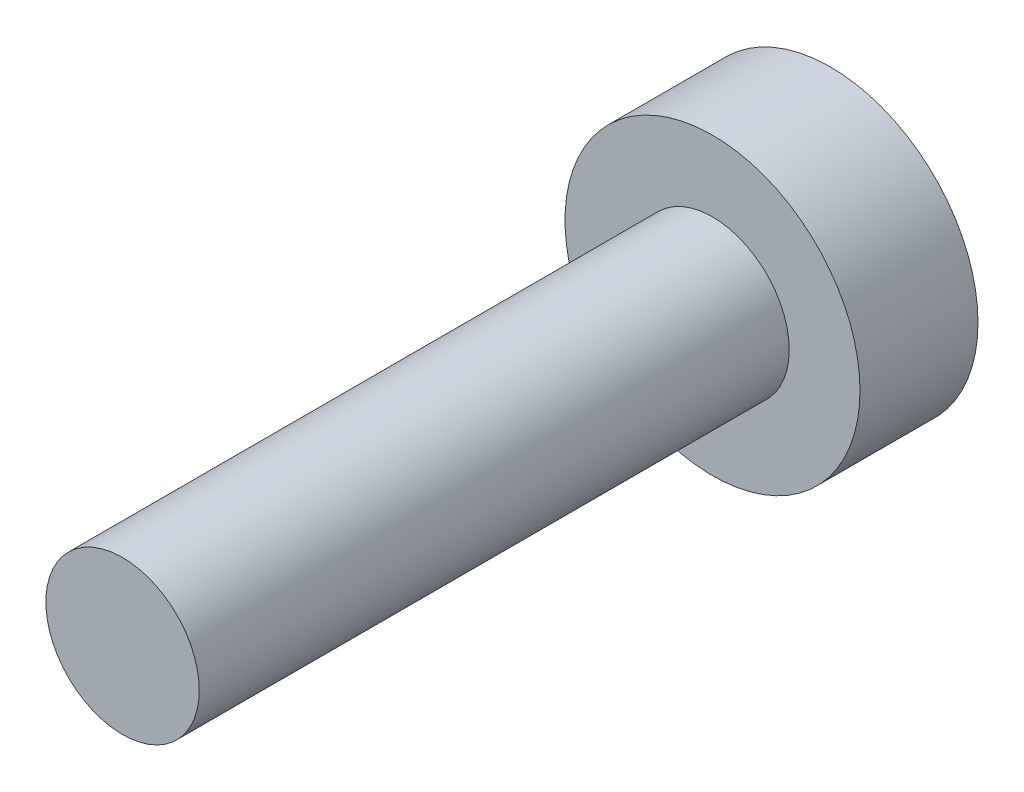
SolidWorks part; units mm, degrees
ref_plane "Front Plane" through (0, 0, 0) normal (0, 0, 1) x (1, 0, 0)
ref_plane "Top Plane" through (0, 0, 0) normal (0, 1, 0) x (1, 0, 0)
ref_plane "Right Plane" through (0, 0, 0) normal (1, 0, 0) x (0, 0, -1)
sketch "Sketch1" plane through (0, 0, 0) normal (0, 0, 1) x (1, 0, 0)
  circle A0 centre (0, 0) radius 1.3
  dimension "D1" = 2.6
extrude "Boss-Extrude1" add sketch "Sketch1" along normal blind 10
sketch "Sketch2" plane through (0, 0, 0) normal (0, 0, 1) x (1, 0, 0)
  circle A0 centre (0, 0) radius 2.5
  dimension "D1" = 5
extrude "Boss-Extrude2" add sketch "Sketch2" against normal blind 2
